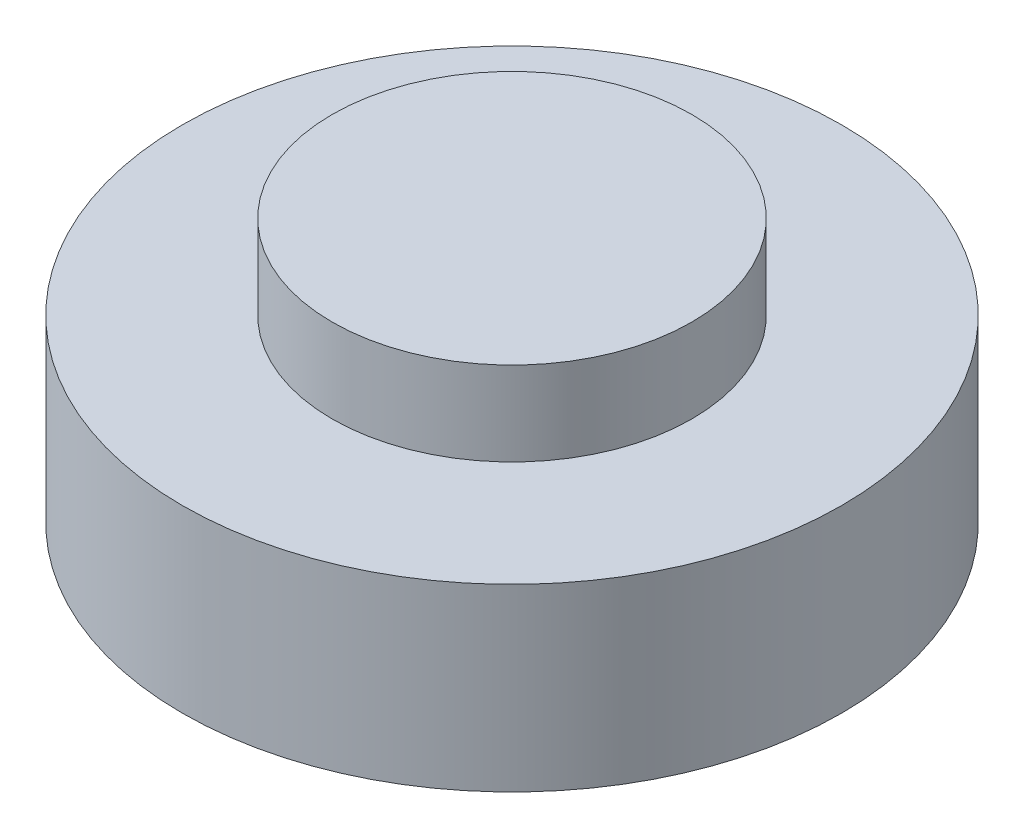
SolidWorks part; units mm, degrees
ref_plane "Front Plane" through (0, 0, 0) normal (0, 0, 1) x (1, 0, 0)
ref_plane "Top Plane" through (0, 0, 0) normal (0, 1, 0) x (1, 0, 0)
ref_plane "Right Plane" through (0, 0, 0) normal (1, 0, 0) x (0, 0, -1)
sketch "Sketch1" plane through (0, 0, 0) normal (0, 1, 0) x (1, 0, 0)
  circle A0 centre (0, 0) radius 27.5
extrude "Boss-Extrude1" add sketch "Sketch1" along normal blind 15
sketch "Sketch2" plane through (0, 15, 0) normal (0, 1, 0) x (1, 0, 0)
  circle A0 centre (0, 0) radius 15
extrude "Boss-Extrude2" add sketch "Sketch2" along normal blind 7
